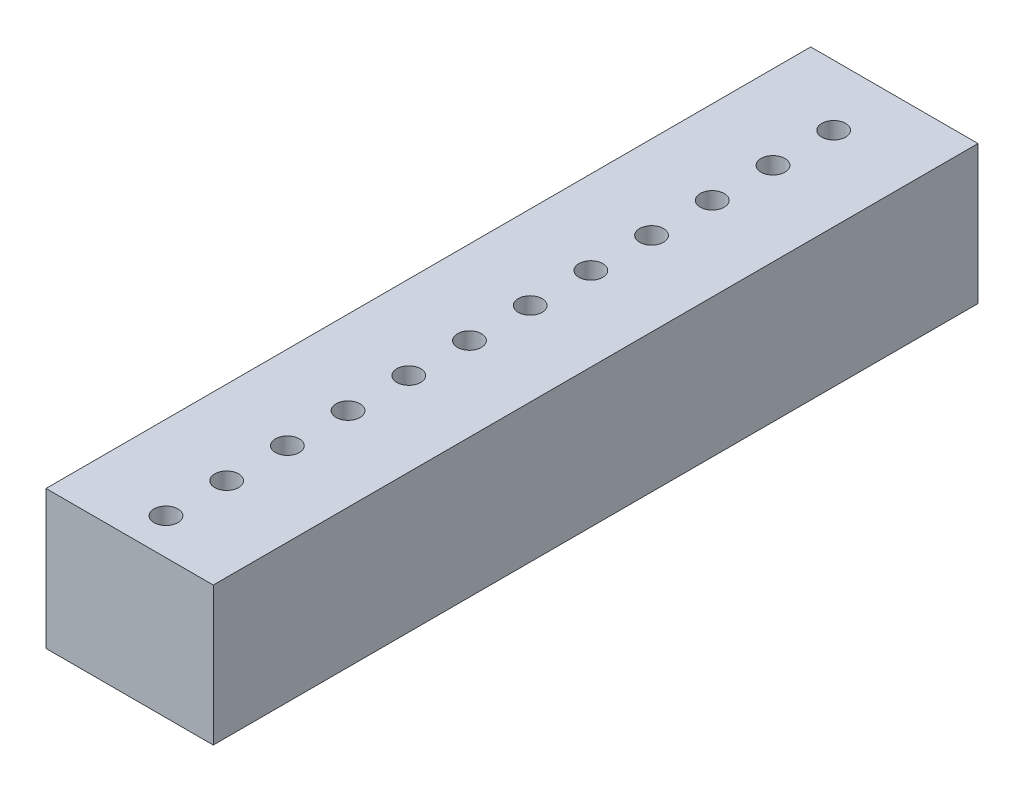
SolidWorks part; units mm, degrees
ref_plane "Front Plane" through (0, 0, 0) normal (0, 0, 1) x (1, 0, 0)
ref_plane "Top Plane" through (0, 0, 0) normal (0, 1, 0) x (1, 0, 0)
ref_plane "Right Plane" through (0, 0, 0) normal (1, 0, 0) x (0, 0, -1)
sketch "Sketch1" plane through (0, 0, 0) normal (0, 1, 0) x (1, 0, 0)
  line L1 (3.5, 16) -> (-3.5, 16)
  line L2 (3.5, 16) -> (3.5, -16)
  line L3 (3.5, -16) -> (-3.5, -16)
  line L4 (-3.5, 16) -> (-3.5, -16)
  line L5 (3.5, 16) -> (-3.5, -16) construction
  line L6 (3.5, -16) -> (-3.5, 16) construction
  line L7 (-0.96, 13.19) -> (1.58, 13.19) construction
  circle A0 centre (0, 13.19) radius 0.5
  circle A1 centre (1.58, 13.19) radius 0.5 construction
  point P0 (0, 0)
  point P10 (0, 0)
  point P11 (0, 14.4964)
  point P12 (0, 13.7019)
  point P13 (0, 16)
  point P18 (0, 14.1207)
  point P19 (0, 13.19)
  dimension "D1" = 7
  dimension "D2" = 32
extrude "Boss-Extrude1" add sketch "Sketch1" along normal mid plane 5.8
sketch "Sketch2" plane through (0, 2.9, 0) normal (0, 1, 0) x (1, 0, 0)
  line L0 (3.5, 16) -> (-3.5, 16) construction
  circle A0 centre (0, 13.46) radius 0.5
  point P2 (0, 14.2298)
  point P3 (0, 0)
  point P4 (0, 14.0805)
  dimension "D1" = 1
  dimension "D2" = 2.54
extrude "Cut-Extrude1" cut sketch "Sketch2" against normal through all
pattern_linear "LPattern1" count 12 spacing 2.54 along (0, 0, 1) of "Cut-Extrude1"
